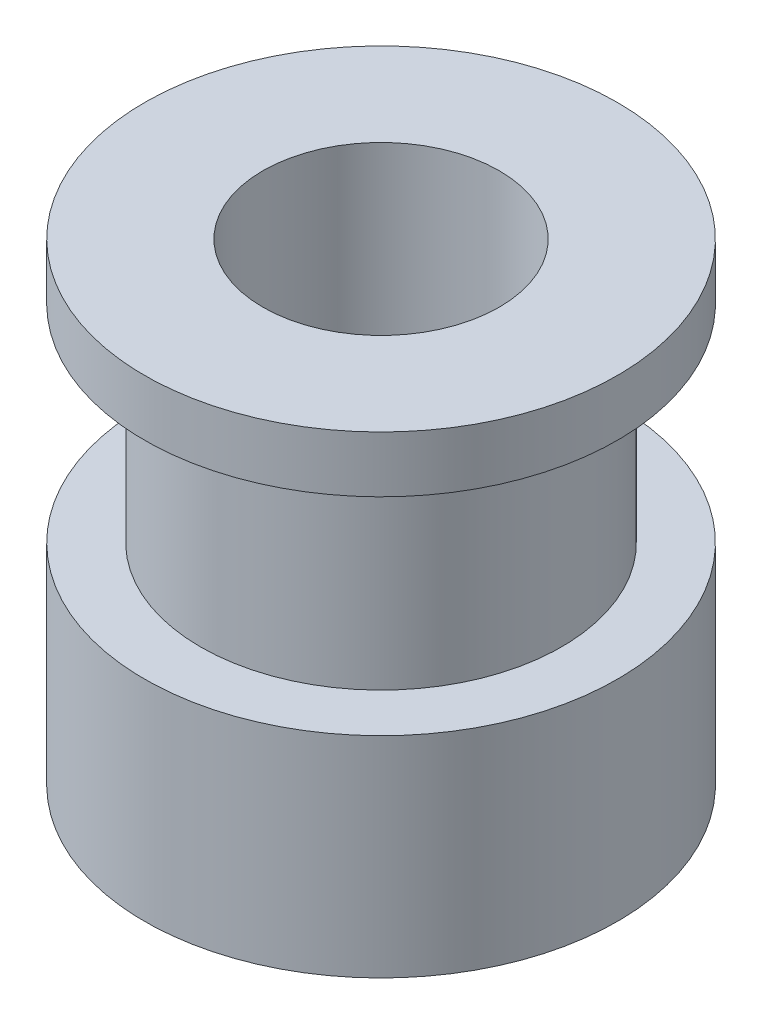
SolidWorks part; units mm, degrees
ref_plane "Front Plane" through (0, 0, 0) normal (0, 0, 1) x (1, 0, 0)
ref_plane "Top Plane" through (0, 0, 0) normal (0, 1, 0) x (1, 0, 0)
ref_plane "Right Plane" through (0, 0, 0) normal (1, 0, 0) x (0, 0, -1)
sketch "Sketch3" plane through (0, 0, 0) normal (1, 0, 0) x (0, 0, -1)
  line L0 (-4, 0) -> (-4, 16)
  line L1 (-4, 16) -> (-8, 16)
  line L2 (-8, 16) -> (-8, 14.1)
  line L3 (-8, 14.1) -> (-6.11, 14.1)
  line L4 (-6.11, 14.1) -> (-6.11, 7.1)
  line L5 (-6.11, 7.1) -> (-8, 7.1)
  line L6 (-8, 7.1) -> (-8, 0)
  line L7 (-8, 0) -> (-4, 0)
  line L8 (0, 0) -> (0, 16) construction
  point P11 (0, 0)
  dimension "D1" = 16
  dimension "D2" = 7.1
  dimension "D3" = 7
  dimension "D4" = 8
  dimension "D5" = 16
  dimension "D6" = 12.22
revolve "Revolve1" add sketch "Sketch3" angle 360 about L8
